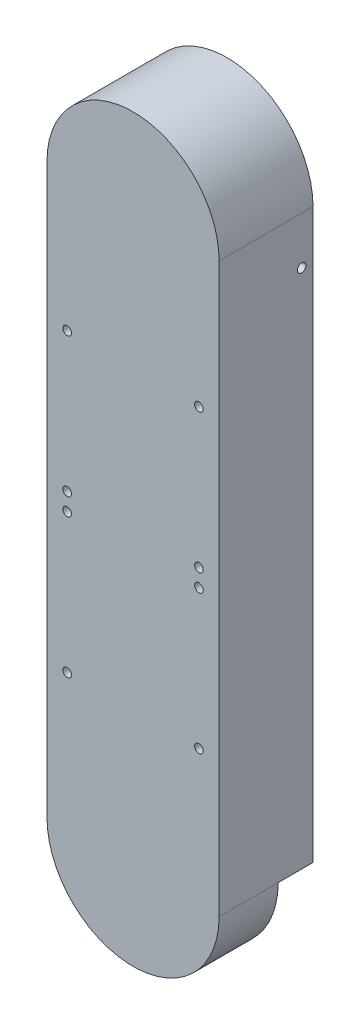
SolidWorks part; units mm, degrees
ref_plane "前视基准面" through (0, 0, 0) normal (0, 0, 1) x (1, 0, 0)
ref_plane "上视基准面" through (0, 0, 0) normal (0, 1, 0) x (1, 0, 0)
ref_plane "右视基准面" through (0, 0, 0) normal (1, 0, 0) x (0, 0, -1)
sketch "草图1" plane through (0, 0, 0) normal (0, 0, 1) x (1, 0, 0)
  line L0 (-30, 0) -> (-30, -115.49)
  line L1 (30, 0) -> (30, -115.49)
  line L3 (35, 0) -> (35, -115.49)
  line L5 (-35, 0) -> (-35, -115.49)
  line L9 (-30, -115.49) -> (30, -115.49) construction
  line L10 (-35, -120.49) -> (35, -120.49) construction
  line L11 (30, -115.49) -> (35, -115.49)
  line L12 (-30, -115.49) -> (-35, -115.49)
  line L13 (35, 0) -> (35, -120.49) construction
  line L14 (-35, 0) -> (-35, -120.49) construction
  arc A0 (30, 0) -> (-30, 0) centre (0, 0) ccw
  arc A1 (35, 0) -> (-35, 0) centre (0, 0) ccw
  dimension "D1" = 60
  dimension "D2" = 115.49
  dimension "D3" = 115.49
  dimension "D4" = 5
extrude "凸台-拉伸1" add sketch "草图1" along normal blind 35
sketch "草图2" plane through (0, 0, 35) normal (0, 0, 1) x (1, 0, 0)
  line L0 (-30, -115.49) -> (30, -115.49)
  line L6 (-35, 0) -> (-35, -115.49)
  line L7 (-35, -115.49) -> (-30, -115.49)
  line L8 (-35, -115.49) -> (-30, -115.49)
  line L9 (30, 0) -> (30, -115.49)
  line L10 (-30, -115.49) -> (-30, 0)
  line L11 (35, -115.49) -> (35, 0)
  line L12 (-35, 0) -> (-35, -115.49)
  line L17 (35, -115.49) -> (35, 0)
  line L20 (30, -115.49) -> (35, -115.49)
  line L21 (30, -115.49) -> (35, -115.49)
  arc A2 (35, 0) -> (-35, 0) centre (0, 0) ccw
  arc A3 (30, 0) -> (-30, 0) centre (0, 0) ccw
  arc A4 (35, 0) -> (-35, 0) centre (0, 0) ccw
  dimension "D1" = 0
extrude "凸台-拉伸2" add sketch "草图2" along normal blind 3.18
sketch "草图3" plane through (0, 0, 0) normal (0, 0, -1) x (-1, 0, 0)
  line L5 (-26.795, -112.09) -> (26.795, -112.09) construction
  line L7 (30, -115.49) -> (-30, -115.49) construction
  circle A0 centre (-26.795, -112.09) radius 1.75
  circle A1 centre (26.795, -112.09) radius 1.75
  point P2 (0, -112.09)
  dimension "D5" = 3.5
  dimension "D6" = 3.5
  dimension "D1" = 3.4
  dimension "D2" = 53.59
extrude "切除-拉伸1" cut sketch "草图3" against normal through all
sketch "草图4" plane through (0, 0, 0) normal (0, 0, -1) x (-1, 0, 0)
  line L4 (-26.795, -55.49) -> (26.795, -55.49) construction
  line L5 (30, -115.49) -> (-30, -115.49) construction
  circle A0 centre (-26.795, -55.49) radius 1.75
  circle A1 centre (26.795, -55.49) radius 1.75
  point P8 (0, -55.49)
  dimension "D3" = 3.5
  dimension "D4" = 3.5
  dimension "D1" = 60
  dimension "D5" = 53.59
extrude "切除-拉伸2" cut sketch "草图4" against normal through all contours A1 | A0
sketch "草图5" plane through (35, 0, 0) normal (1, 0, 0) x (0, 0, -1)
  line L0 (-38.18, 0) -> (0, 0) construction
  line L1 (0, -115.49) -> (0, 0) construction
  circle A0 centre (-4.61, -19.28) radius 1.75
  dimension "D1" = 3.5
  dimension "D2" = 19.28
  dimension "D3" = 4.61
extrude "切除-拉伸3" cut sketch "草图5" against normal through all
sketch "草图6" plane through (0, -115.49, 0) normal (0, -1, 0) x (1, 0, 0)
  line L8 (30, 0) -> (35, 0)
  line L9 (35, 0) -> (35, 38.18)
  line L10 (35, 38.18) -> (-35, 38.18)
  line L11 (-35, 38.18) -> (-35, 0)
  line L12 (-35, 0) -> (-30, 0)
  line L13 (-30, 0) -> (-30, 35)
  line L14 (-30, 35) -> (30, 35)
  line L15 (30, 35) -> (30, 0)
  line L16 (30, 0) -> (35, 0)
  line L17 (35, 0) -> (35, 38.18)
  line L18 (35, 38.18) -> (-35, 38.18)
  line L19 (-35, 38.18) -> (-35, 0)
  line L20 (-35, 0) -> (-30, 0)
  line L21 (-30, 0) -> (-30, 35)
  line L22 (-30, 35) -> (30, 35)
  line L23 (30, 35) -> (30, 0)
  dimension "D1" = 0
extrude "凸台-拉伸3" add sketch "草图6" along normal blind 115.49
sketch "草图10" plane through (0, 0, 38.18) normal (0, 0, 1) x (1, 0, 0)
  line L0 (35, -230.98) -> (-35, -230.98) construction
  line L1 (35, -230.98) -> (-35, -230.98)
  arc A1 (-35, -230.98) -> (35, -230.98) centre (0, -230.98) ccw
  dimension "D2" = 70
extrude "凸台-拉伸7" add sketch "草图10" against normal blind 24
sketch "草图11" plane through (0, 0, 14.18) normal (0, 0, -1) x (-1, 0, 0)
  line L0 (-30, -230.98) -> (30, -230.98) construction
  circle A0 centre (0, -230.98) radius 25
  dimension "D1" = 50
extrude "切除-拉伸4" cut sketch "草图11" against normal up to surface (20.82 mm away) up to face at (-25.045, -55.49, 35)
sketch "草图12" plane through (0, 0, 38.18) normal (0, 0, 1) x (1, 0, 0)
  line L0 (-26.795, -112.09) -> (-26.795, -119.23) construction
  line L1 (26.795, -112.09) -> (26.795, -119.23) construction
  circle A0 centre (26.795, -119.23) radius 1.75
  circle A1 centre (-26.795, -119.23) radius 1.75
  dimension "D3" = 3.5
  dimension "D4" = 3.5
  dimension "D1" = 7.14
  dimension "D2" = 7.14
extrude "切除-拉伸5" cut sketch "草图12" against normal through all
sketch "草图13" plane through (0, 0, 38.18) normal (0, 0, 1) x (1, 0, 0)
  line L0 (-26.795, -119.23) -> (-26.795, -175.86) construction
  line L1 (26.795, -119.23) -> (26.795, -175.86) construction
  circle A0 centre (-26.795, -175.86) radius 1.75
  circle A1 centre (26.795, -175.86) radius 1.75
  dimension "D3" = 3.5
  dimension "D4" = 3.5
  dimension "D1" = 56.63
  dimension "D2" = 56.63
extrude "切除-拉伸6" cut sketch "草图13" against normal blind 24
